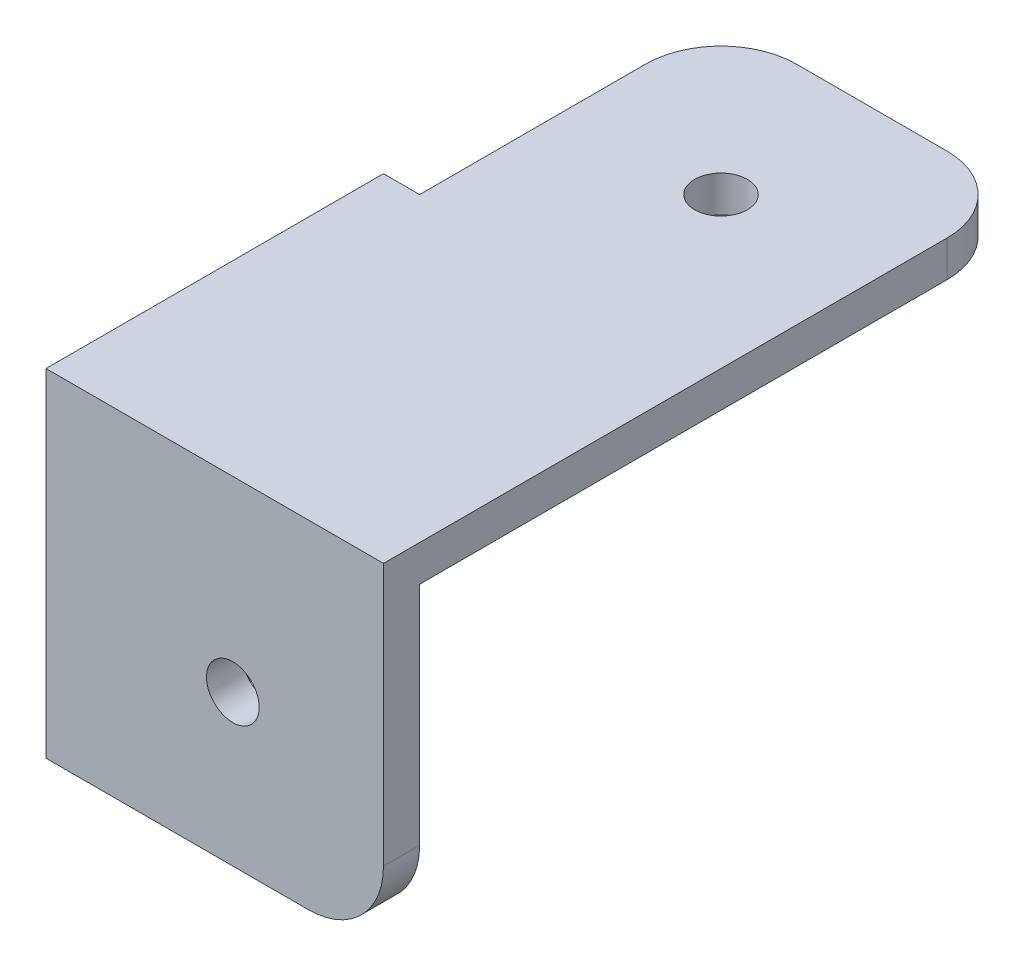
SolidWorks part; units mm, degrees
ref_plane "Front Plane" through (0, 0, 0) normal (0, 0, 1) x (1, 0, 0)
ref_plane "Top Plane" through (0, 0, 0) normal (0, 1, 0) x (1, 0, 0)
ref_plane "Right Plane" through (0, 0, 0) normal (1, 0, 0) x (0, 0, -1)
sketch "Sketch1" plane through (0, 0, 0) normal (0, 1, 0) x (1, 0, 0)
  line L0 (-2.4, 0) -> (-2.4, -2.4) construction
  line L1 (0, 0) -> (20, 0)
  line L2 (0, 0) -> (0, -2.4)
  line L3 (0, -2.4) -> (20, -2.4)
  line L4 (20, 0) -> (20, -2.4)
  line L5 (0, 0) -> (-2.4, 0)
  line L6 (0, 0) -> (0, 20)
  line L7 (0, 20) -> (-2.4, 20)
  line L8 (-2.4, 0) -> (-2.4, 20)
  line L13 (-2.4, -2.4) -> (0, -2.4) construction
  line L14 (-2.4, 0) -> (-2.4, -2.4)
  line L15 (-2.4, -2.4) -> (0, -2.4)
  line L16 (-2.4, 0) -> (0, 0)
  dimension "D1" = 20
  dimension "D2" = 2.4
  dimension "D3" = 2.4
  dimension "D4" = 20
extrude "Boss-Extrude1" add sketch "Sketch1" against normal blind 20 contours L8 L5 L6 L7 | L14 L15 L2 L5 | L4 L1 L2 L3
sketch "Sketch2" plane through (0, 0, 0) normal (0, 1, 0) x (1, 0, 0)
  line L0 (20, -2.4) -> (20, 40)
  line L5 (20, 40) -> (0, 40)
  line L6 (0, 40) -> (0, 20)
  line L7 (0, 20) -> (-2.4, 20)
  line L8 (-2.4, 20) -> (-2.4, -2.4)
  line L9 (-2.4, -2.4) -> (20, -2.4)
  line L10 (0, 0) -> (20, 0) construction
  dimension "D1" = 40
extrude "Boss-Extrude2" add sketch "Sketch2" along normal blind 2.4
sketch "Sketch4" plane through (0, 0, 0) normal (1, 0, 0) x (0, 0, -1)
  line L0 (10, 0) -> (10, -20) construction
  line L1 (0, 0) -> (20, 0) construction
  line L2 (0, -20) -> (20, -20) construction
  circle A0 centre (10, -10) radius 1.75
  dimension "D1" = 3.5
sketch "Sketch5" plane through (0, 0, 0) normal (0, 0, -1) x (-1, 0, 0)
  line L0 (-10, 0) -> (-10, -20) construction
  line L1 (0, 0) -> (-20, 0) construction
  line L2 (0, -20) -> (-20, -20) construction
  circle A0 centre (-10, -10) radius 1.75
  dimension "D1" = 3.5
extrude "Cut-Extrude1" cut sketch "Sketch4" against normal up to next
extrude "Cut-Extrude2" cut sketch "Sketch5" against normal up to next
sketch "Sketch6" plane through (0, 2.4, 0) normal (0, 1, 0) x (1, 0, 0)
  line L0 (0, 30) -> (20, 30) construction
  line L1 (0, 40) -> (0, 20) construction
  line L2 (20, -2.4) -> (20, 40) construction
  circle A0 centre (10, 30) radius 1.75
  dimension "D1" = 3.5
extrude "Cut-Extrude3" cut sketch "Sketch6" against normal up to next
sketch "Sketch7" plane through (0, 0, 0) normal (0, -1, 0) x (1, 0, 0)
  line L0 (0, -10) -> (20, -10) construction
  line L1 (0, 0) -> (0, -20) construction
  line L2 (20, 0) -> (20, -40) construction
  circle A0 centre (10, -10) radius 2
  dimension "D1" = 4
extrude "Boss-Extrude3" add sketch "Sketch7" along normal blind 5
fillet "Fillet1" radius 5 4 edges at (20, -20, 1.2) (-1.2, -20, -20) (20, 1.2, -40) (0, 1.2, -40)
